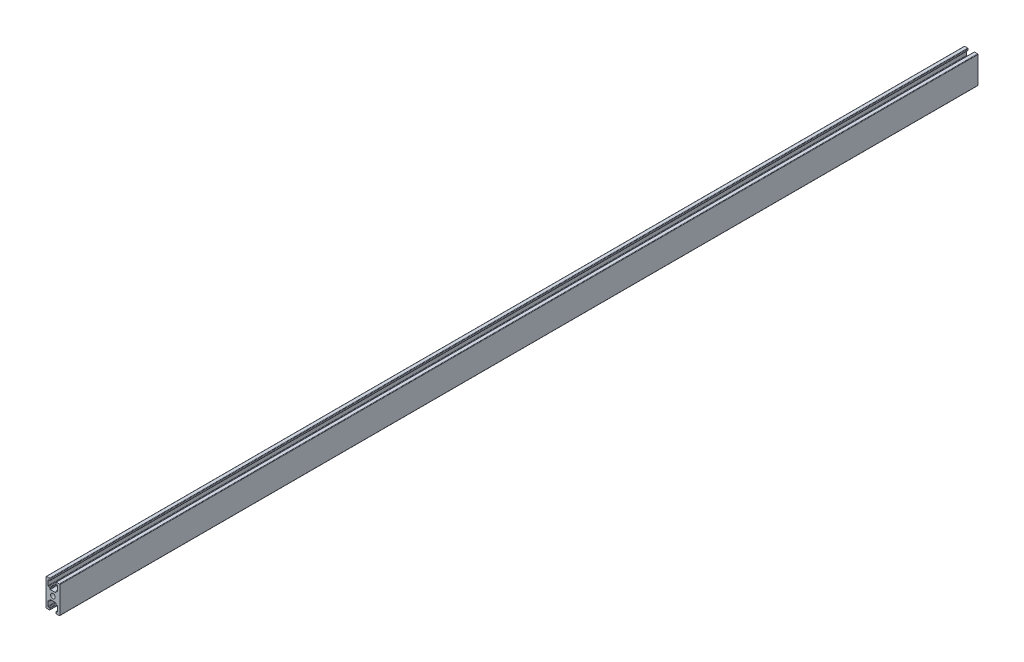
SolidWorks part; units mm, degrees
material "6063 T5"
ref_plane "Спереди" through (0, 0, 0) normal (0, 0, 1) x (1, 0, 0)
ref_plane "Сверху" through (0, 0, 0) normal (0, 1, 0) x (1, 0, 0)
ref_plane "Справа" through (0, 0, 0) normal (1, 0, 0) x (0, 0, -1)
sketch "Эскиз2" plane through (0, 0, 0) normal (0, 0, 1) x (1, 0, 0)
  line L0 (-7.6042, 14.9774) -> (-7.6042, -15.0226) construction
  line L15 (0, 4.7) -> (0, -4.7) construction
  line L16 (-5.25, 15) -> (-7, 15)
  line L17 (-7.5, 14.5) -> (-7.5, -14.5)
  line L18 (-7, -15) -> (-5.25, -15)
  line L19 (5.25, -15) -> (7, -15)
  line L20 (7.5, -14.5) -> (7.5, 14.5)
  line L21 (7, 15) -> (5.25, 15)
  circle A0 centre (0, 0) radius 2.5
  arc A1 (7, -15) -> (7.5, -14.5) centre (7, -14.5) ccw
  arc A2 (-7.5, -14.5) -> (-7, -15) centre (-7, -14.5) ccw
  arc A3 (7.5, 14.5) -> (7, 15) centre (7, 14.5) ccw
  arc A4 (-7, 15) -> (-7.5, 14.5) centre (-7, 14.5) ccw
  point P6 (0, 0)
  line B0 (-5.25, 15) -> (-3.75, 15)
  line B1 (-3.25, 14.5) -> (-3.25, 13.2)
  line B2 (-3.75, 12.7) -> (-4.75, 12.7)
  line B3 (-5.25, 12.2) -> (-5.25, 7.2)
  line B4 (-4.75, 6.7) -> (-3.75, 6.7)
  line B5 (-3.25, 6.2) -> (-3.25, 5.2)
  line B6 (-2.75, 4.7) -> (2.75, 4.7)
  line B7 (3.25, 5.2) -> (3.25, 6.2)
  line B8 (3.75, 6.7) -> (4.75, 6.7)
  line B9 (5.25, 7.2) -> (5.25, 12.2)
  line B10 (4.75, 12.7) -> (3.75, 12.7)
  line B11 (3.25, 13.2) -> (3.25, 14.5)
  line B12 (3.75, 15) -> (5.25, 15)
  line B13 (5.25, 15) -> (-5.25, 15) construction
  arc B14 (3.25, 14.5) -> (3.75, 15) centre (3.75, 14.5) cw
  arc B15 (3.75, 12.7) -> (3.25, 13.2) centre (3.75, 13.2) cw
  arc B16 (5.25, 12.2) -> (4.75, 12.7) centre (4.75, 12.2) ccw
  arc B17 (4.75, 6.7) -> (5.25, 7.2) centre (4.75, 7.2) ccw
  arc B18 (3.25, 6.2) -> (3.75, 6.7) centre (3.75, 6.2) cw
  arc B19 (2.75, 4.7) -> (3.25, 5.2) centre (2.75, 5.2) ccw
  arc B20 (-3.25, 5.2) -> (-2.75, 4.7) centre (-2.75, 5.2) ccw
  arc B21 (-3.75, 6.7) -> (-3.25, 6.2) centre (-3.75, 6.2) cw
  arc B22 (-5.25, 7.2) -> (-4.75, 6.7) centre (-4.75, 7.2) ccw
  arc B23 (-4.75, 12.7) -> (-5.25, 12.2) centre (-4.75, 12.2) ccw
  arc B24 (-3.25, 13.2) -> (-3.75, 12.7) centre (-3.75, 13.2) cw
  arc B25 (-3.75, 15) -> (-3.25, 14.5) centre (-3.75, 14.5) cw
  line B26 (5.25, -15) -> (3.75, -15)
  line B27 (3.25, -14.5) -> (3.25, -13.2)
  line B28 (3.75, -12.7) -> (4.75, -12.7)
  line B29 (5.25, -12.2) -> (5.25, -7.2)
  line B30 (4.75, -6.7) -> (3.75, -6.7)
  line B31 (3.25, -6.2) -> (3.25, -5.2)
  line B32 (2.75, -4.7) -> (-2.75, -4.7)
  line B33 (-3.25, -5.2) -> (-3.25, -6.2)
  line B34 (-3.75, -6.7) -> (-4.75, -6.7)
  line B35 (-5.25, -7.2) -> (-5.25, -12.2)
  line B36 (-4.75, -12.7) -> (-3.75, -12.7)
  line B37 (-3.25, -13.2) -> (-3.25, -14.5)
  line B38 (-3.75, -15) -> (-5.25, -15)
  line B39 (-5.25, -15) -> (5.25, -15) construction
  arc B40 (-3.25, -14.5) -> (-3.75, -15) centre (-3.75, -14.5) cw
  arc B41 (-3.75, -12.7) -> (-3.25, -13.2) centre (-3.75, -13.2) cw
  arc B42 (-5.25, -12.2) -> (-4.75, -12.7) centre (-4.75, -12.2) ccw
  arc B43 (-4.75, -6.7) -> (-5.25, -7.2) centre (-4.75, -7.2) ccw
  arc B44 (-3.25, -6.2) -> (-3.75, -6.7) centre (-3.75, -6.2) cw
  arc B45 (-2.75, -4.7) -> (-3.25, -5.2) centre (-2.75, -5.2) ccw
  arc B46 (3.25, -5.2) -> (2.75, -4.7) centre (2.75, -5.2) ccw
  arc B47 (3.75, -6.7) -> (3.25, -6.2) centre (3.75, -6.2) cw
  arc B48 (5.25, -7.2) -> (4.75, -6.7) centre (4.75, -7.2) ccw
  arc B49 (4.75, -12.7) -> (5.25, -12.2) centre (4.75, -12.2) ccw
  arc B50 (3.25, -13.2) -> (3.75, -12.7) centre (3.75, -13.2) cw
  arc B51 (3.75, -15) -> (3.25, -14.5) centre (3.75, -14.5) cw
  dimension "D2" = 5
  dimension "D5" = 0.5
  dimension "D1" = 30
  dimension "D3" = 30
  dimension "D4" = 15
sketch_block_instance "Блок1-1"
sketch_block "Блок1" parameters "D6"=0.5, "D1"=10.5, "D2"=6.5, "D3"=2.3, "D4"=8.3, "D5"=2
sketch_block_instance "Блок1-2"
extrude "Бобышка-Вытянуть1" add sketch "Эскиз2" along normal blind 1000 contours B51 B26 L19 A1 L20 A3 L21 B12 B14 B11 B15 B10 B16 B9 B17 B8 B18 B7 B19 B6 B20 B5 B21 B4 B22 B3 B23 B2 B24 B1 B25 B0 L16 A4 L17 A2 L18 B38 B40 B37 B41 B36 B42 B35 B43 B34 B44 B33 B45 B32 B46
